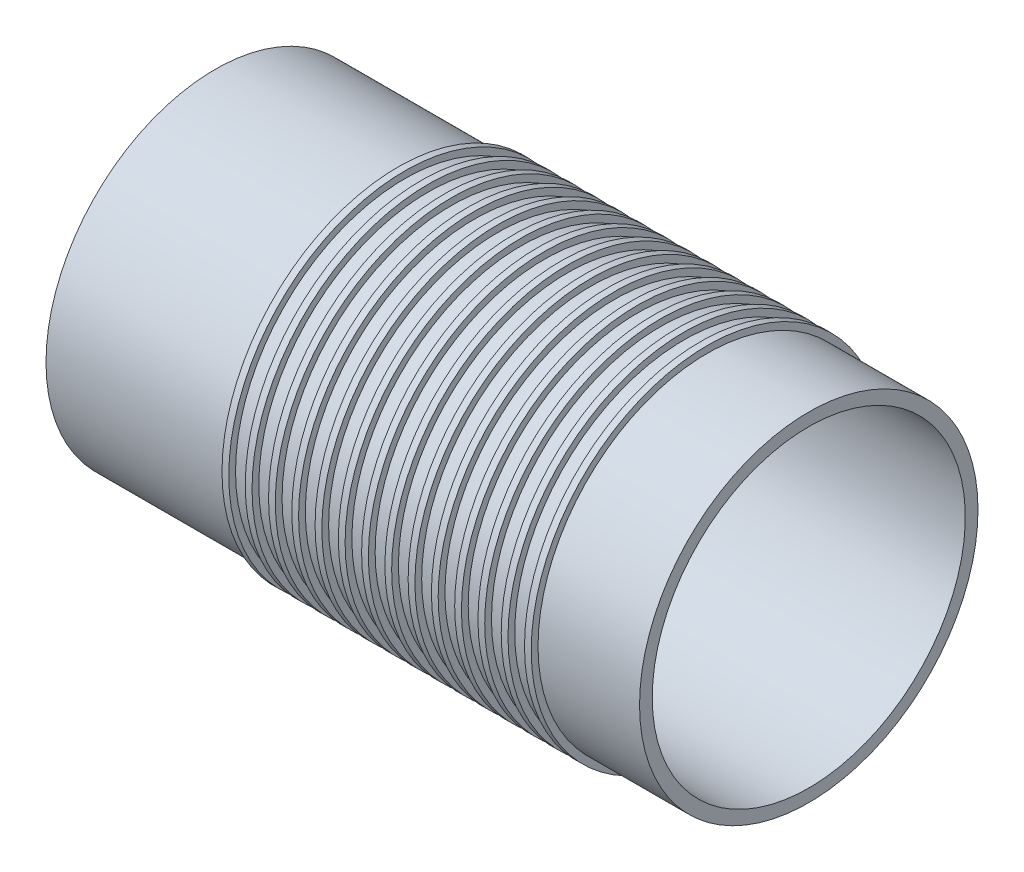
SolidWorks part; units mm, degrees
ref_plane "Front Plane" through (0, 0, 0) normal (0, 0, 1) x (1, 0, 0)
ref_plane "Top Plane" through (0, 0, 0) normal (0, 1, 0) x (1, 0, 0)
ref_plane "Right Plane" through (0, 0, 0) normal (1, 0, 0) x (0, 0, -1)
sketch "Sketch1" plane through (0, 0, 0) normal (0, 0, 1) x (1, 0, 0)
  line L0 (-100.1879, 0) -> (96.0625, 0) construction
  line L1 (55, 0) -> (-55, 0) construction
  line L2 (-35.075, 18.5) -> (35.075, 18.5)
  line L3 (0, 0) -> (0, 61.2914) construction
  line L4 (0, -55) -> (0, 55) construction
  line L5 (35.075, 18.5) -> (35.075, 20)
  line L6 (35.075, 20) -> (23.075, 20)
  line L7 (23.075, 20) -> (23.075, 20.8)
  line L8 (23.075, 20.8) -> (22.275, 20.8)
  line L9 (22.275, 20.8) -> (22.275, 20)
  line L10 (22.275, 20) -> (20.325, 20)
  line L11 (-35.075, 18.5) -> (-35.075, 20)
  line L12 (19.525, 20.8) -> (19.525, 20)
  line L13 (20.325, 20.8) -> (19.525, 20.8)
  line L14 (20.325, 20) -> (20.325, 20.8)
  line L15 (16.775, 20.8) -> (16.775, 20)
  line L16 (17.575, 20.8) -> (16.775, 20.8)
  line L17 (17.575, 20) -> (17.575, 20.8)
  line L18 (14.025, 20.8) -> (14.025, 20)
  line L19 (14.825, 20.8) -> (14.025, 20.8)
  line L20 (14.825, 20) -> (14.825, 20.8)
  line L21 (11.275, 20.8) -> (11.275, 20)
  line L22 (12.075, 20.8) -> (11.275, 20.8)
  line L23 (12.075, 20) -> (12.075, 20.8)
  line L24 (8.525, 20.8) -> (8.525, 20)
  line L25 (9.325, 20.8) -> (8.525, 20.8)
  line L26 (9.325, 20) -> (9.325, 20.8)
  line L27 (5.775, 20.8) -> (5.775, 20)
  line L28 (6.575, 20.8) -> (5.775, 20.8)
  line L29 (6.575, 20) -> (6.575, 20.8)
  line L30 (3.025, 20.8) -> (3.025, 20)
  line L31 (3.825, 20.8) -> (3.025, 20.8)
  line L32 (3.825, 20) -> (3.825, 20.8)
  line L33 (0.275, 20.8) -> (0.275, 20)
  line L34 (1.075, 20.8) -> (0.275, 20.8)
  line L35 (1.075, 20) -> (1.075, 20.8)
  line L36 (-2.475, 20.8) -> (-2.475, 20)
  line L37 (-1.675, 20.8) -> (-2.475, 20.8)
  line L38 (-1.675, 20) -> (-1.675, 20.8)
  line L39 (-5.225, 20.8) -> (-5.225, 20)
  line L40 (-4.425, 20.8) -> (-5.225, 20.8)
  line L41 (-4.425, 20) -> (-4.425, 20.8)
  line L42 (-7.975, 20.8) -> (-7.975, 20)
  line L43 (-7.175, 20.8) -> (-7.975, 20.8)
  line L44 (-7.175, 20) -> (-7.175, 20.8)
  line L45 (-10.725, 20.8) -> (-10.725, 20)
  line L46 (-9.925, 20.8) -> (-10.725, 20.8)
  line L47 (-9.925, 20) -> (-9.925, 20.8)
  line L48 (-13.475, 20.8) -> (-13.475, 20)
  line L49 (-12.675, 20.8) -> (-13.475, 20.8)
  line L50 (-12.675, 20) -> (-12.675, 20.8)
  line L78 (22.275, 20.8) -> (19.525, 20.8) construction
  line L79 (19.525, 20) -> (17.575, 20)
  line L80 (16.775, 20) -> (14.825, 20)
  line L81 (14.025, 20) -> (12.075, 20)
  line L82 (11.275, 20) -> (9.325, 20)
  line L83 (8.525, 20) -> (6.575, 20)
  line L84 (5.775, 20) -> (3.825, 20)
  line L85 (3.025, 20) -> (1.075, 20)
  line L86 (0.275, 20) -> (-1.675, 20)
  line L87 (-2.475, 20) -> (-4.425, 20)
  line L88 (-5.225, 20) -> (-7.175, 20)
  line L89 (-7.975, 20) -> (-9.925, 20)
  line L90 (-10.725, 20) -> (-12.675, 20)
  line L96 (-13.475, 20) -> (-35.075, 20)
  line L176 (-29.975, 20.8) -> (-29.975, 20)
  line L177 (-29.175, 20.8) -> (-29.975, 20.8)
  line L178 (-29.175, 20) -> (-29.175, 20.8)
  line L179 (-32.725, 20.8) -> (-32.725, 20)
  line L180 (-31.925, 20.8) -> (-32.725, 20.8)
  line L181 (-31.925, 20) -> (-31.925, 20.8)
  line L182 (-35.475, 20.8) -> (-35.475, 20)
  line L183 (-34.675, 20.8) -> (-35.475, 20.8)
  line L184 (-34.675, 20) -> (-34.675, 20.8)
  line L185 (-38.225, 20.8) -> (-38.225, 20)
  line L186 (-37.425, 20.8) -> (-38.225, 20.8)
  line L187 (-37.425, 20) -> (-37.425, 20.8)
  line L188 (-40.975, 20.8) -> (-40.975, 20)
  line L189 (-40.175, 20.8) -> (-40.975, 20.8)
  line L190 (-40.175, 20) -> (-40.175, 20.8)
  line L191 (-43.725, 20.8) -> (-43.725, 20)
  line L192 (-42.925, 20.8) -> (-43.725, 20.8)
  line L193 (-42.925, 20) -> (-42.925, 20.8)
  line L194 (-46.475, 20.8) -> (-46.475, 20)
  line L195 (-45.675, 20.8) -> (-46.475, 20.8)
  line L196 (-45.675, 20) -> (-45.675, 20.8)
  line L197 (-16.225, 20.8) -> (-16.225, 20)
  line L198 (-15.425, 20.8) -> (-16.225, 20.8)
  line L199 (-15.425, 20) -> (-15.425, 20.8)
  line L200 (-18.975, 20.8) -> (-18.975, 20)
  line L201 (-18.175, 20.8) -> (-18.975, 20.8)
  line L202 (-18.175, 20) -> (-18.175, 20.8)
  line L203 (-21.725, 20.8) -> (-21.725, 20)
  line L204 (-20.925, 20.8) -> (-21.725, 20.8)
  line L205 (-20.925, 20) -> (-20.925, 20.8)
  line L206 (-24.475, 20.8) -> (-24.475, 20)
  line L207 (-23.675, 20.8) -> (-24.475, 20.8)
  line L208 (-23.675, 20) -> (-23.675, 20.8)
  line L209 (-27.225, 20.8) -> (-27.225, 20)
  line L210 (-26.425, 20.8) -> (-27.225, 20.8)
  line L211 (-26.425, 20) -> (-26.425, 20.8)
  dimension "D1" = 40
  dimension "D2" = 1.5
  dimension "D3" = 41.6
  dimension "D4" = 0.8
  dimension "D5" = 12
  dimension "D6" = 70.15
  dimension "D8" = 2.75
  dimension "D7" = 26
revolve "Revolve1" add sketch "Sketch1" angle 360 about L0
